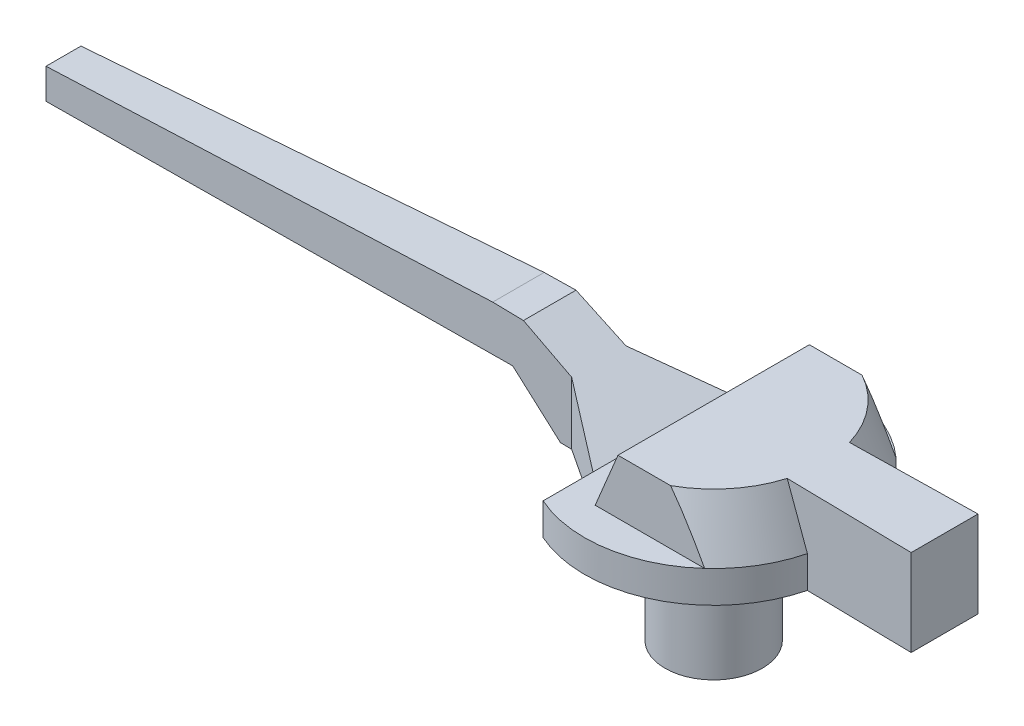
SolidWorks part; units mm, degrees
material "ABS PC"
ref_plane "Front Plane" through (0, 0, 0) normal (0, 0, 1) x (1, 0, 0)
ref_plane "Top Plane" through (0, 0, 0) normal (0, 1, 0) x (1, 0, 0)
ref_plane "Right Plane" through (0, 0, 0) normal (1, 0, 0) x (0, 0, -1)
sketch "Эскиз1" plane through (0, 0, 0) normal (1, 0, 0) x (0, 0, -1)
  line L0 (0, 0) -> (0, -10.2074) construction
  line L1 (-0.45, 0) -> (-1.6, 0)
  line L2 (-1.6, 0) -> (-1.6, 4)
  line L3 (-1.6, 4) -> (-4.25, 4)
  line L4 (-4.25, 4) -> (-4.25, 5.05)
  line L5 (-4.25, 5.05) -> (-3.5949, 6.85)
  line L6 (-3.5949, 6.85) -> (0, 6.85)
  line L7 (0, 6.85) -> (0, 5)
  line L8 (0, 5) -> (-0.45, 5)
  line L9 (-0.45, 5) -> (-0.45, 0)
  dimension "D1" = 0.9
  dimension "D2" = 3.2
  dimension "D3" = 8.5
  dimension "D4" = 4
  dimension "D5" = 6.85
  dimension "D6" = 1.05
  dimension "D7" = 20
  dimension "D8" = 5
revolve "Повернуть1" add sketch "Эскиз1" angle 360 about L0
sketch "Эскиз2" plane through (0, 6.85, 0) normal (0, 1, 0) x (1, 0, 0)
  line L0 (0, 0) -> (-21.9741, 0) construction
  line L1 (-21.4, -0.575) -> (-21.4, 0.575)
  line L2 (-21.4, 0.575) -> (7.6, 1.1)
  line L3 (7.6, 1.1) -> (7.6, -1.1)
  line L4 (-21.4, -0.575) -> (7.6, -1.1)
  circle A0 centre (0, 0) radius 4.25 construction
  point P8 (7.6, 0)
  point P9 (-21.4, 0)
  dimension "D1" = 2.2
  dimension "D2" = 1.15
  dimension "D3" = 29
  dimension "D4" = 7.6
extrude "Бобышка-Вытянуть1" add sketch "Эскиз2" against normal up to surface (2.85 mm away) up to face at (0, 4, 1.6)
sketch "Эскиз3" plane through (0, 6.85, 0) normal (0, 1, 0) x (1, 0, 0)
  line L1 (-22.7341, 3.15) -> (22.7341, 3.15)
  line L2 (-22.7341, 3.15) -> (-22.7341, -3.15)
  line L3 (-22.7341, -3.15) -> (22.7341, -3.15)
  line L4 (22.7341, 3.15) -> (22.7341, -3.15)
  line L5 (-22.7341, 3.15) -> (22.7341, -3.15) construction
  line L6 (-22.7341, -3.15) -> (22.7341, 3.15) construction
  point P0 (0, 0)
  dimension "D1" = 6.3
extrude "Вырез-Вытянуть1" cut sketch "Эскиз3" against normal up to vertex (1.8 mm away) flip side to cut
sketch "Эскиз4" plane through (0, 0, 3.15) normal (0, 0, 1) x (1, 0, 0)
  line L0 (0, 6.85) -> (-0.7493, 5.05)
  line L1 (-1.7322, 6.85) -> (1.7322, 6.85) construction
  line L2 (-2.8531, 5.05) -> (2.8531, 5.05) construction
  line L3 (-0.7493, 5.05) -> (-1.7322, 5.05)
  line L4 (-1.7322, 5.05) -> (-5.3953, 6.85)
  line L5 (-21.4, 6.85) -> (-3.4805, 6.85) construction
  line L6 (-5.3953, 6.85) -> (0, 6.85)
  line L7 (-6.4251, 6.85) -> (-21.4, 5.95)
  line L8 (-21.4, 4) -> (-21.4, 6.85) construction
  line L9 (-21.4, 5.95) -> (-21.4, 6.85)
  line L10 (-21.4, 6.85) -> (-6.4251, 6.85)
  line L11 (-21.4, 4.95) -> (-5.7568, 5.373)
  line L12 (-5.7568, 5.373) -> (-4.1564, 4)
  line L13 (-4.1564, 4) -> (-21.4, 4)
  line L14 (-21.4, 4) -> (-21.4, 4.95)
  dimension "D1" = 1
extrude "Вырез-Вытянуть2" cut sketch "Эскиз4" against normal through all
sketch "Эскиз5" plane through (0, 5.05, 0) normal (0, 1, 0) x (1, 0, 0)
  line L0 (0, 0) -> (11.1663, 0) construction
  line L1 (0, 3.15) -> (0, -3.15) construction
  line L2 (-1.7322, 4.791) -> (-1.7322, 2.2397)
  line L3 (-1.7322, 3.15) -> (-1.7322, -3.15) construction
  line L4 (-1.7322, 2.2397) -> (-3.7795, 0.894)
  line L6 (-3.7795, 4.791) -> (-1.7322, 4.791)
  line L11 (-3.7795, 0.894) -> (-5.3953, 0.8647)
  line L12 (-5.3953, 0.8647) -> (-3.7795, 4.791)
  line L13 (-5.3953, -0.8647) -> (-3.7795, -4.791)
  line L14 (-3.7795, -0.894) -> (-5.3953, -0.8647)
  line L15 (-3.7795, -4.791) -> (-1.7322, -4.791)
  line L16 (-1.7322, -2.2397) -> (-3.7795, -0.894)
  line L17 (-1.7322, -4.791) -> (-1.7322, -2.2397)
extrude "Вырез-Вытянуть4" cut sketch "Эскиз5" against normal through all both and the other way through all
